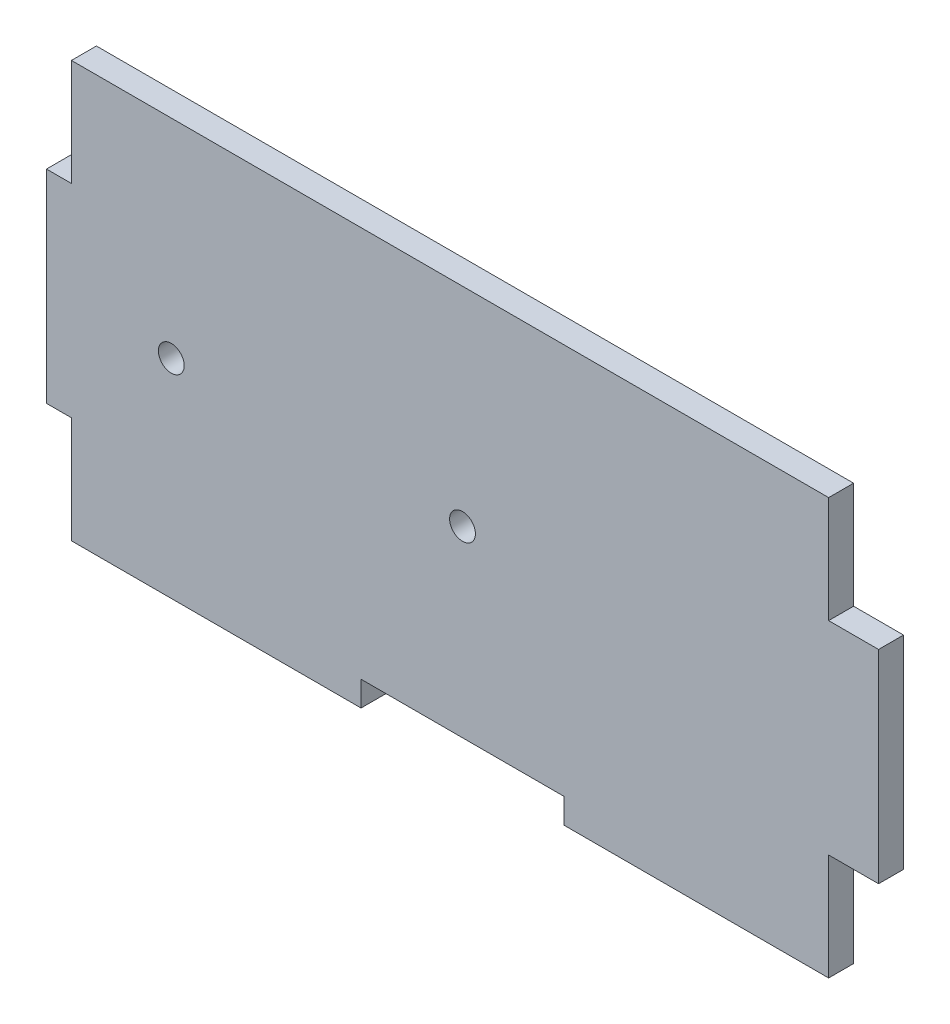
SolidWorks part; units mm, degrees
ref_plane "Alzado" through (0, 0, 0) normal (0, 0, 1) x (1, 0, 0)
ref_plane "Planta" through (0, 0, 0) normal (0, 1, 0) x (1, 0, 0)
ref_plane "Vista lateral" through (0, 0, 0) normal (1, 0, 0) x (0, 0, -1)
sketch "Model" plane through (0, 0, 0) normal (0, 0, 1) x (1, 0, 0)
  line L0 (186, 103) -> (186, 90.195)
  line L1 (186, 90.195) -> (183, 90.195)
  line L2 (183, 90.195) -> (183, 65.805)
  line L3 (183, 65.805) -> (186, 65.805)
  line L4 (186, 65.805) -> (186, 53)
  line L5 (186, 53) -> (220.805, 53)
  line L6 (220.805, 53) -> (220.805, 56)
  line L7 (220.805, 56) -> (245.195, 56)
  line L8 (245.195, 56) -> (245.195, 53)
  line L9 (245.195, 53) -> (269.585, 53)
  line L10 (269.585, 53) -> (280, 53)
  line L11 (280, 53) -> (280, 65.805)
  line L12 (280, 65.805) -> (283, 65.805)
  line L13 (283, 65.805) -> (283, 90.195)
  line L14 (283, 90.195) -> (280, 90.195)
  line L15 (280, 90.195) -> (280, 103)
  line L16 (280, 103) -> (186, 103)
extrude "Saliente-Extruir1" add sketch "Model" along normal blind 3
sketch "Croquis2" plane through (0, 0, 3) normal (0, 0, 1) x (1, 0, 0)
  line L0 (233, 103) -> (233, 56) construction
  line L1 (280, 103) -> (186, 103) construction
  line L2 (220.805, 56) -> (245.195, 56) construction
  line L3 (183, 78) -> (283, 78) construction
  line L4 (183, 90.195) -> (183, 65.805) construction
  line L5 (283, 65.805) -> (283, 90.195) construction
  circle A0 centre (233, 78) radius 1.55
  circle A1 centre (198, 78) radius 1.55
  dimension "D1" = 3.1
  dimension "D2" = 3.1
  dimension "D3" = 35
extrude "Cortar-Extruir1" cut sketch "Croquis2" against normal blind 3
sketch "Croquis3" plane through (0, 0, 3) normal (0, 0, 1) x (1, 0, 0)
  line L0 (233, 76.45) -> (233, 78) construction
  line L1 (233, 78) -> (231.45, 78) construction
  line L2 (198, 76.45) -> (198, 78) construction
  line L3 (198, 78) -> (196.45, 78) construction
  circle A0 centre (233, 78) radius 1.55 construction
  circle A1 centre (198, 78) radius 1.55 construction
sketch "Croquis4" plane through (0, 0, 3) normal (0, 0, 1) x (1, 0, 0)
  line L0 (280, 103) -> (186, 103) construction
  line L1 (280, 90.195) -> (277, 90.195)
  line L2 (280, 90.195) -> (280, 103)
  line L3 (280, 103) -> (277, 103)
  line L4 (277, 90.195) -> (277, 103)
  line L5 (280, 53) -> (280, 65.805) construction
  line L6 (280, 65.805) -> (277, 65.805)
  line L7 (280, 65.805) -> (280, 53)
  line L8 (280, 53) -> (277, 53)
  line L9 (277, 65.805) -> (277, 53)
  line L10 (245.195, 53) -> (280, 53) construction
  point P15 (280, 65.805)
  dimension "D1" = 3
  dimension "D2" = 3
extrude "Cortar-Extruir2" cut sketch "Croquis4" against normal blind 10
